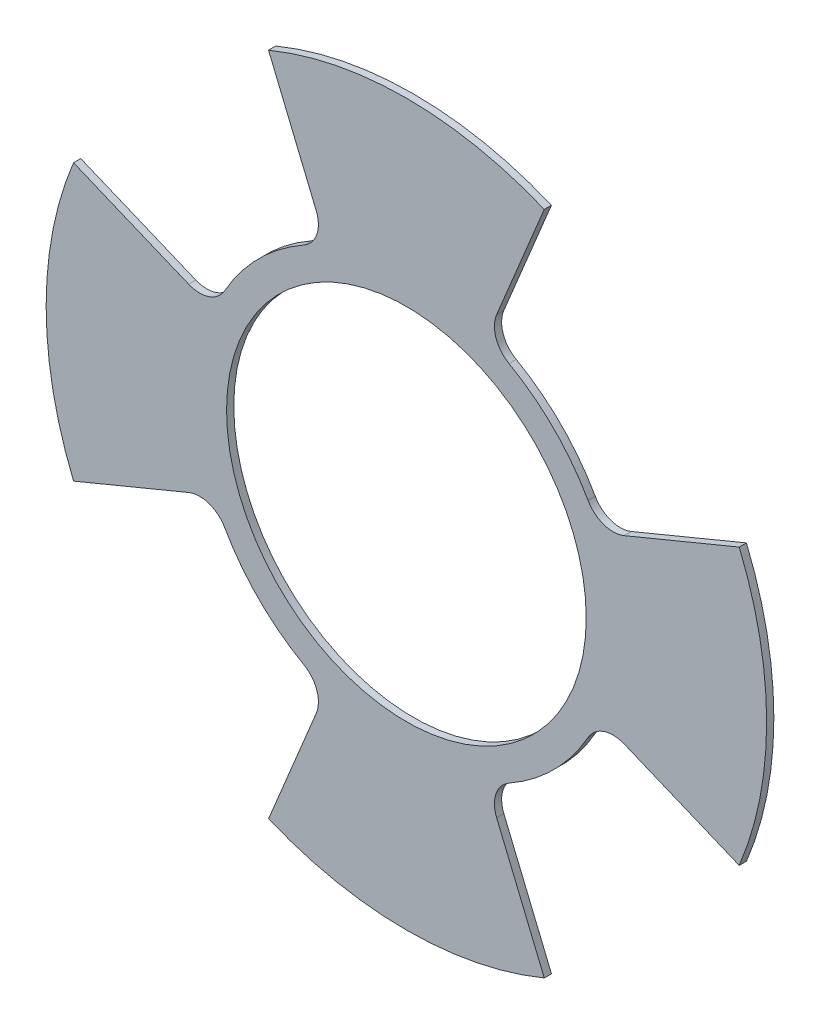
SolidWorks part; units mm, degrees
ref_plane "Front Plane" through (0, 0, 0) normal (0, 0, 1) x (1, 0, 0)
ref_plane "Top Plane" through (0, 0, 0) normal (0, 1, 0) x (1, 0, 0)
ref_plane "Right Plane" through (0, 0, 0) normal (1, 0, 0) x (0, 0, -1)
sketch "Sketch1" plane through (0, 0, 0) normal (0, 0, 1) x (1, 0, 0)
  circle A0 centre (0, 0) radius 39.624
  circle A1 centre (0, 0) radius 79.375
  dimension "D1" = 158.75
  dimension "D2" = 79.248
extrude "Boss-Extrude1" add sketch "Sketch1" along normal blind 1.5875
sketch "Sketch2" plane through (0, 0, 1.5875) normal (0, 0, 1) x (1, 0, 0)
  circle A0 centre (0, 0) radius 45.974
  circle A1 centre (0, 0) radius 79.375
  circle A2 centre (0, 0) radius 79.375 construction
  circle A3 centre (0, 0) radius 39.624 construction
  dimension "D1" = 0
  dimension "D2" = 6.35
extrude "Cut-Extrude1" cut sketch "Sketch2" against normal through all
sketch "Sketch3" plane through (0, 0, 1.5875) normal (0, 0, 1) x (1, 0, 0)
  line L0 (-30.3755, 73.3329) -> (-17.5935, 42.4744)
  line L1 (30.3755, 73.3329) -> (17.5935, 42.4744)
  line L2 (-17.5935, 42.4744) -> (0, 0) construction
  line L3 (0, 0) -> (17.5935, 42.4744) construction
  line L4 (-30.3755, 73.3329) -> (30.3755, 73.3329) construction
  line L5 (0, 73.3329) -> (0, 0) construction
  circle A1 centre (0, 0) radius 45.974 construction
  arc A3 (17.5935, 42.4744) -> (-17.5935, 42.4744) centre (0, 0) ccw
  circle A6 centre (0, 0) radius 79.375
  point P6 (0, 0)
  circle M6 centre (0, 0) radius 45.974
  dimension "D2" = 158.75
  dimension "D1" = 45
extrude "Boss-Extrude2" add sketch "Sketch3" against normal up to surface (1.5875 mm away) contours L1 A6 L0 M6
fillet "Fillet1" radius 6.35 2 edges at (-17.5935, 42.4744, 0.7937) (17.5935, 42.4744, 0.7937)
pattern_circular "CirPattern1" count 4 over 360 about axis through (0, 0, 0) along (0, 0, 1) of "Boss-Extrude2", "Fillet1"
